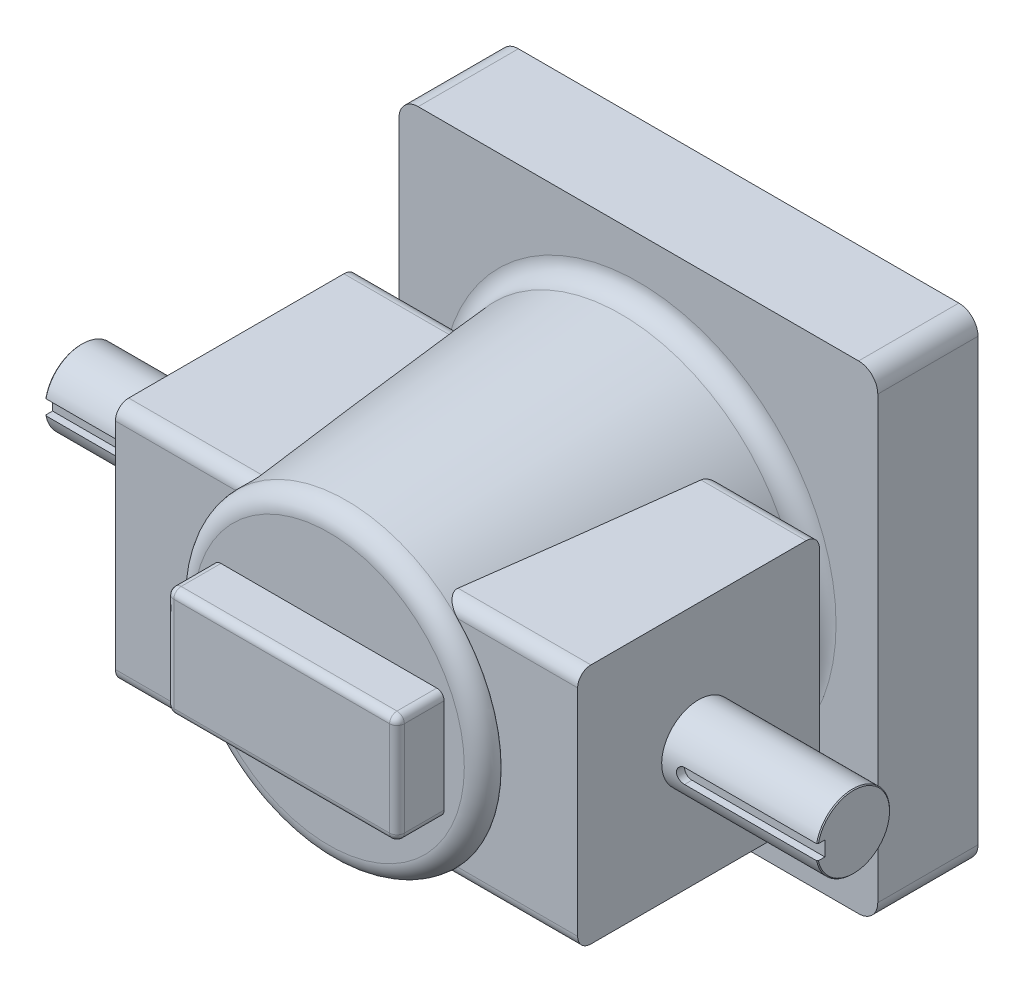
SolidWorks part; units mm, degrees
ref_plane "Front Plane" through (0, 0, 0) normal (0, 0, 1) x (1, 0, 0)
ref_plane "Top Plane" through (0, 0, 0) normal (0, 1, 0) x (1, 0, 0)
ref_plane "Right Plane" through (0, 0, 0) normal (1, 0, 0) x (0, 0, -1)
ref_plane "D" through (0, 0, 116.84) normal (0, 0, 1) x (1, 0, 0)
ref_plane "G" through (0, 0, 196.85) normal (0, 0, 1) x (1, 0, 0)
sketch "Sketch1" plane through (0, 0, 0) normal (0, 0, 1) x (1, 0, 0)
  line L0 (-103.124, -103.124) -> (103.124, 103.124) construction
  line L1 (-103.124, 103.124) -> (103.124, 103.124)
  line L2 (-103.124, 103.124) -> (-103.124, -103.124)
  line L3 (-103.124, -103.124) -> (103.124, -103.124)
  line L4 (103.124, 103.124) -> (103.124, -103.124)
  dimension "D1" = 206.248
extrude "C dim" add sketch "Sketch1" along normal blind 43.18
ref_plane "F" through (166.37, 0, 0) normal (1, 0, 0) x (0, 0, -1)
sketch "A" plane through (0, 0, 0) normal (1, 0, 0) x (0, 0, -1)
  line L0 (-116.84, 47.2186) -> (-116.84, -47.2186) construction
  line L1 (-116.84, 0) -> (0, 0) construction
  circle A0 centre (-116.84, 0) radius 15.875
  dimension "D1" = 31.75
extrude "Shaft" add sketch "A" along normal up to surface (153.67 mm away) from offset 12.7 separate body up to plane "F"
ref_plane "E" through (99.568, 0, 0) normal (1, 0, 0) x (0, 0, -1)
sketch "Sketch3" plane through (0, 0, 0) normal (1, 0, 0) x (0, 0, -1)
  line L0 (-64.77, -52.07) -> (-168.91, 52.07) construction
  line L1 (-64.77, 52.07) -> (-168.91, 52.07)
  line L2 (-64.77, 52.07) -> (-64.77, -52.07)
  line L3 (-64.77, -52.07) -> (-168.91, -52.07)
  line L4 (-168.91, 52.07) -> (-168.91, -52.07)
  line L6 (0, 103.124) -> (-43.18, 103.124) construction
  line L7 (-43.18, 103.124) -> (-21.59, 103.124) construction
  line L8 (-64.77, 52.07) -> (-43.18, 52.07) construction
  line L9 (-43.18, 103.124) -> (-43.18, -103.124) construction
  point P4 (-116.84, 0)
extrude "Boss-Extrude3" add sketch "Sketch3" along normal up to surface (99.568 mm away) separate body up to plane "E"
mirror "Mirror2" about plane through (0, 0, 0) normal (1, 0, 0) of bodies 103
fillet "Fillet1" radius 5.715 4 edges at (49.784, -52.07, 64.77) (49.784, -52.07, 168.91) (49.784, 52.07, 64.77) (49.784, 52.07, 168.91)
fillet "Fillet4" radius 5.715 4 edges at (-49.784, -52.07, 64.77) (-49.784, -52.07, 168.91) (-49.784, 52.07, 64.77) (-49.784, 52.07, 168.91)
sketch "Sketch4" plane through (0, 0, 43.18) normal (0, 0, 1) x (1, 0, 0)
  line L0 (0, 52.07) -> (0, 103.124) construction
  line L1 (0, 52.07) -> (0, -52.07) construction
  line L3 (103.124, 103.124) -> (-103.124, 103.124) construction
  line L4 (-99.568, 52.07) -> (99.568, 52.07) construction
  circle A0 centre (0, 0) radius 77.597
  point P7 (0, 77.597)
extrude "Boss-Extrude4" add sketch "Sketch4" along normal offset from surface 7.62 draft 5
fillet "Fillet2" radius 8.255 6 edges at (-65.9304, 0, 176.53) (103.124, -103.124, 21.59) (-103.124, -103.124, 21.59) (-103.124, 103.124, 21.59) (103.124, 103.124, 21.59) (77.597, 0, 43.18)
sketch "Sketch5" plane through (0, 0, 176.53) normal (0, 0, 1) x (1, 0, 0)
  line L0 (0, 0) -> (52.2042, 0) construction
  line L1 (-52.2042, 26.1021) -> (52.2042, 26.1021) construction
  line L2 (-52.2042, 26.1021) -> (-52.2042, -26.1021) construction
  line L3 (-52.2042, -26.1021) -> (52.2042, -26.1021) construction
  line L4 (52.2042, 26.1021) -> (52.2042, -26.1021) construction
  line L5 (-49.6642, 23.5621) -> (49.6642, 23.5621)
  line L6 (49.6642, 23.5621) -> (49.6642, -23.5621)
  line L7 (-49.6642, -23.5621) -> (49.6642, -23.5621)
  line L8 (-49.6642, 23.5621) -> (-49.6642, -23.5621)
  circle A0 centre (0, 0) radius 58.3661 construction
  dimension "D1" = 2.54
extrude "Boss-Extrude5" add sketch "Sketch5" along normal up to surface (20.32 mm away) up to plane "G"
chamfer "Chamfer1" distance 0.381 angle 45 1 edges at (166.37, 0, 100.965)
fillet "Fillet3" radius 3.175 8 edges at (0, -23.5621, 196.85) (49.6642, 0, 196.85) (0, 23.5621, 196.85) (-49.6642, 0, 196.85) (-49.6642, -23.5621, 186.69) (49.6642, -23.5621, 186.69) (-49.6642, 23.5621, 186.69) (49.6642, 23.5621, 186.69)
sketch "Sketch6" plane through (0, 0, 116.84) normal (0, 0, 1) x (1, 0, 0)
  line L0 (166.37, 0) -> (109.093, 0) construction
  line L1 (166.37, -15.494) -> (166.37, 15.494) construction
  line L2 (166.37, -3.175) -> (109.093, -3.175)
  line L3 (166.37, 3.175) -> (109.093, 3.175)
  line L4 (105.918, 0) -> (99.568, 0) construction
  line L6 (109.093, 3.175) -> (109.093, -3.175) construction
  line L7 (99.568, 46.355) -> (99.568, -46.355) construction
  arc A0 (166.37, -3.175) -> (166.37, 3.175) centre (166.37, 0) ccw
  arc A1 (109.093, 3.175) -> (109.093, -3.175) centre (109.093, 0) ccw
  point P5 (137.7315, 0)
  dimension "D1" = 6.35
extrude "B" cut sketch "Sketch6" along normal through all from offset 12.3698
mirror "Mirror6" about plane through (0, 0, 0) normal (1, 0, 0) of bodies 108
combine bodies "Combine1" operation type add bodies to combine 107 108 109
